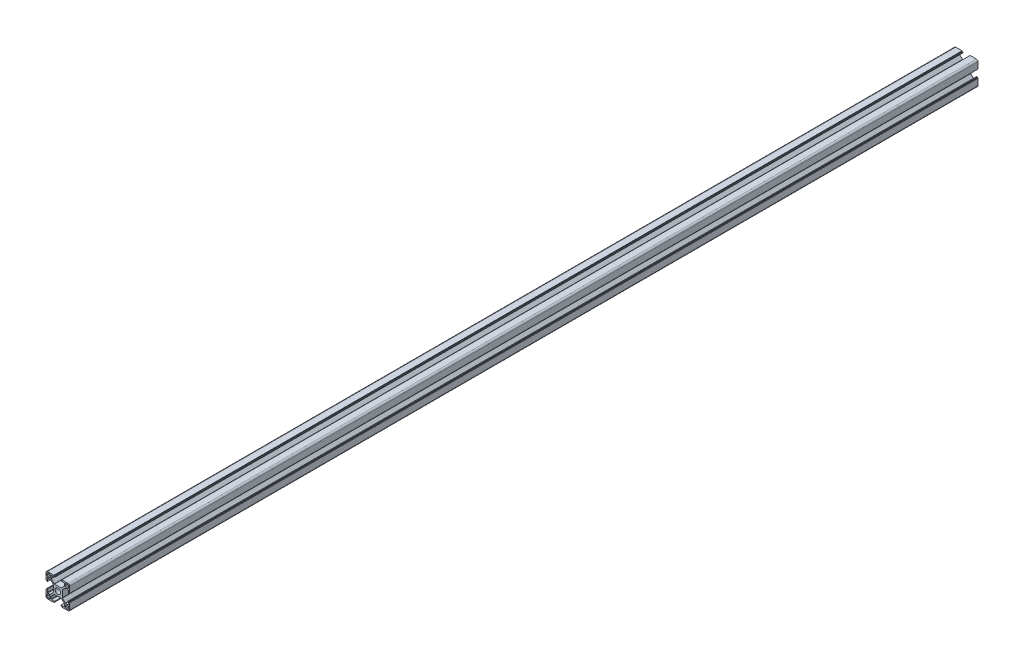
SolidWorks part; units mm, degrees
ref_plane "前视基准面" through (0, 0, 0) normal (0, 0, 1) x (1, 0, 0)
ref_plane "上视基准面" through (0, 0, 0) normal (0, 1, 0) x (1, 0, 0)
ref_plane "右视基准面" through (0, 0, 0) normal (1, 0, 0) x (0, 0, -1)
sketch "草图1" plane through (0, 0, 0) normal (0, 0, 1) x (1, 0, 0)
  line L0 (0, 0) -> (0, 65.3905) construction
  line L1 (0, 0) -> (64.2648, 0) construction
  line L2 (0, 0) -> (79.9729, 79.9729) construction
  line L3 (5.7, 0) -> (5.7, 4.4272)
  line L4 (5.7, 4.4272) -> (9.6728, 8.4)
  line L5 (9.6728, 8.4) -> (13.2, 8.4)
  line L6 (13.2, 8.4) -> (13.2, 4.1)
  line L7 (13.2, 4.1) -> (14.1, 4.1)
  line L8 (14.1, 4.1) -> (14.1, 5.1)
  line L9 (14.1, 5.1) -> (15, 5.1)
  line L10 (15, 5.1) -> (15, 15)
  line L11 (5.1, 15) -> (15, 15)
  line L12 (5.1, 14.1) -> (5.1, 15)
  line L13 (4.1, 14.1) -> (5.1, 14.1)
  line L14 (4.1, 13.2) -> (4.1, 14.1)
  line L15 (8.4, 13.2) -> (4.1, 13.2)
  line L16 (8.4, 9.6728) -> (8.4, 13.2)
  line L17 (4.4272, 5.7) -> (8.4, 9.6728)
  line L18 (0, 5.7) -> (4.4272, 5.7)
  line L20 (9.7, 9.7) -> (13.7, 9.7)
  line L21 (9.7, 9.7) -> (9.7, 13.7)
  line L22 (9.7, 13.7) -> (13.7, 13.7)
  line L23 (13.7, 9.7) -> (13.7, 13.7)
  line L24 (9.7, 9.7) -> (13.7, 13.7) construction
  line L25 (9.7, 13.7) -> (13.7, 9.7) construction
  line L26 (0, 5.7) -> (0, 0)
  line L27 (0, 0) -> (5.7, 0)
  point P9 (11.7, 11.7)
  dimension "D1" = 45
  dimension "D2" = 5.7
  dimension "D3" = 1.8
  dimension "D4" = 0.9
  dimension "D5" = 8.2
  dimension "D6" = 10.2
  dimension "D7" = 1.8
  dimension "D8" = 15
  dimension "D9" = 16.8
  dimension "D10" = 4
  dimension "D11" = 1.3
extrude "凸台-拉伸1" add sketch "草图1" along normal blind 1150 contours L3 L4 L5 L6 L7 L8 L9 L10 L11 L12 L13 L14 L15 L16 L17 L18 L26 L27
fillet "圆角1" radius 1 4 edges at (9.7, 9.7, 575) (13.7, 9.7, 575) (9.7, 13.7, 575) (13.7, 13.7, 575)
fillet "圆角2" radius 2 1 edges at (15, 15, 575)
fillet "圆角3" radius 0.5 6 edges at (5.7, 4.4272, 575) (4.4272, 5.7, 575) (8.4, 13.2, 575) (8.4, 9.6728, 575) (9.6728, 8.4, 575) (13.2, 8.4, 575)
pattern_circular "阵列(圆周)1" count 4 over 360 about axis through (0, 0, 0) along (0, 0, 1) of "圆角2", "圆角3", "凸台-拉伸1", "圆角1"
sketch "草图2" plane through (0, 0, 1150) normal (0, 0, 1) x (1, 0, 0)
  circle A0 centre (0, 0) radius 3.4
  dimension "D1" = 6.8
extrude "切除-拉伸1" cut sketch "草图2" against normal through all
sketch "草图3" plane through (0, 0, 0) normal (0, 1, 0) x (1, 0, 0)
  line L0 (-198.1932, -575) -> (209.0128, -575) construction
  line L1 (-5.1, 0) -> (-13, 0) construction
  line L2 (-5.1, -1150) -> (-13, -1150) construction
  line L3 (0, 279.4776) -> (0, -1139.4124) construction
  circle A0 centre (0, -70) radius 3.05
  circle A1 centre (0, -220) radius 3.05
  circle A2 centre (0, -930) radius 3.05
  circle A3 centre (0, -1080) radius 3.05
  dimension "D1" = 150
  dimension "D2" = 6.1
  dimension "D3" = 860
extrude "切除-拉伸2" cut sketch "草图3" against normal mid plane 20
sketch "草图4" plane through (0, 0, 0) normal (1, 0, 0) x (0, 0, -1)
  line L0 (-580, 172.8387) -> (-580, -163.0114) construction
  line L1 (27.6714, 0) -> (-1361.7279, 0) construction
  line L3 (-1150, 5.1) -> (-1150, 13) construction
  circle A0 centre (-610, 0) radius 2.6
  circle A1 centre (-550, 0) radius 2.6
  circle A2 centre (-490, 0) radius 2.4335
  circle A3 centre (-445, 0) radius 2.3713
  dimension "D1" = 5.2
  dimension "D2" = 60
  dimension "D4" = 45
  dimension "D3" = 570
  dimension "D5" = 90
extrude "切除-拉伸3" cut sketch "草图4" against normal mid plane 200
